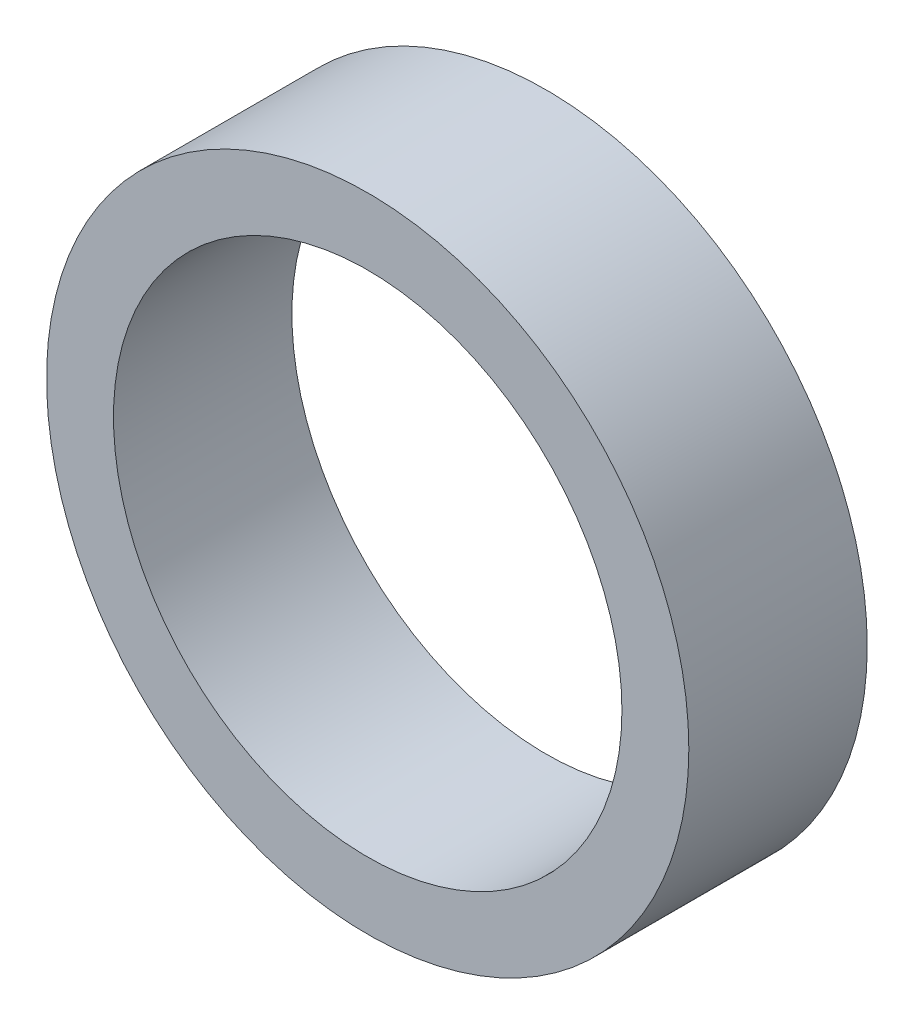
SolidWorks part; units mm, degrees
ref_plane "Plan de face" through (0, 0, 0) normal (0, 0, 1) x (1, 0, 0)
ref_plane "Plan de dessus" through (0, 0, 0) normal (0, 1, 0) x (1, 0, 0)
ref_plane "Plan de droite" through (0, 0, 0) normal (1, 0, 0) x (0, 0, -1)
sketch "Esquisse1" plane through (0, 0, 0) normal (0, 0, 1) x (1, 0, 0)
  circle A0 centre (0, 0) radius 14.25
  circle A1 centre (0, 0) radius 18
  dimension "D1" = 28.5
  dimension "D2" = 36
extrude "Extrusion1" add sketch "Esquisse1" along normal mid plane 10
